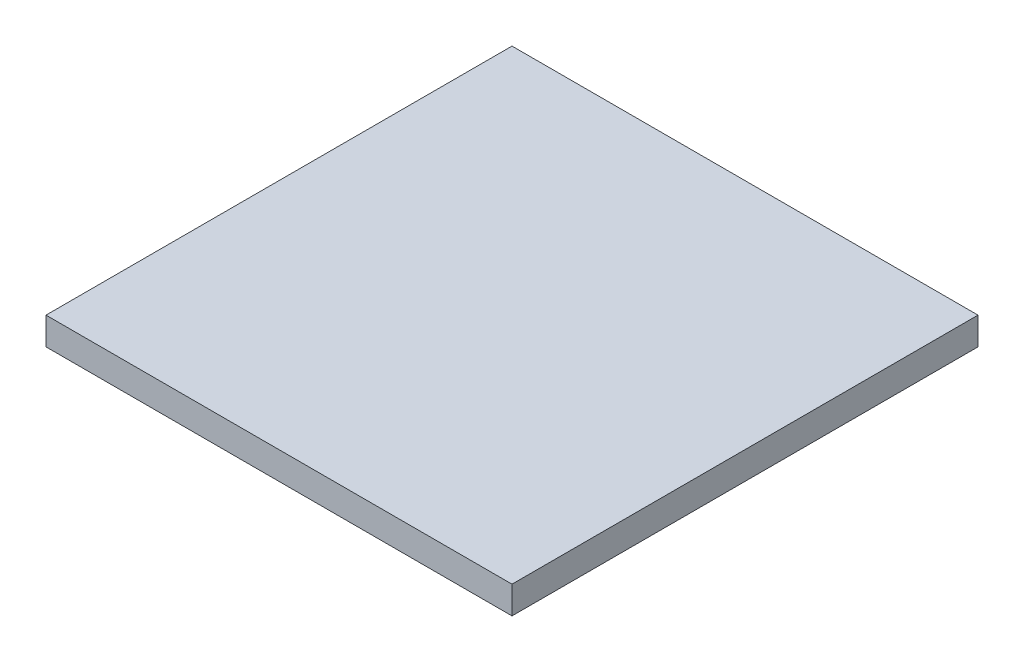
SolidWorks part; units mm, degrees
ref_plane "前视基准面" through (0, 0, 0) normal (0, 0, 1) x (1, 0, 0)
ref_plane "上视基准面" through (0, 0, 0) normal (0, 1, 0) x (1, 0, 0)
ref_plane "右视基准面" through (0, 0, 0) normal (1, 0, 0) x (0, 0, -1)
sketch "草图1" plane through (0, 0, 0) normal (0, 1, 0) x (1, 0, 0)
  line L1 (-12.7, -12.7) -> (12.7, -12.7)
  line L2 (-12.7, -12.7) -> (-12.7, 12.7)
  line L3 (-12.7, 12.7) -> (12.7, 12.7)
  line L4 (12.7, -12.7) -> (12.7, 12.7)
  line L5 (-12.7, -12.7) -> (12.7, 12.7) construction
  line L6 (-12.7, 12.7) -> (12.7, -12.7) construction
  point P0 (0, 0)
  dimension "D1" = 25.4
  dimension "D2" = 25.4
extrude "凸台-拉伸1" add sketch "草图1" along normal blind 1.5
